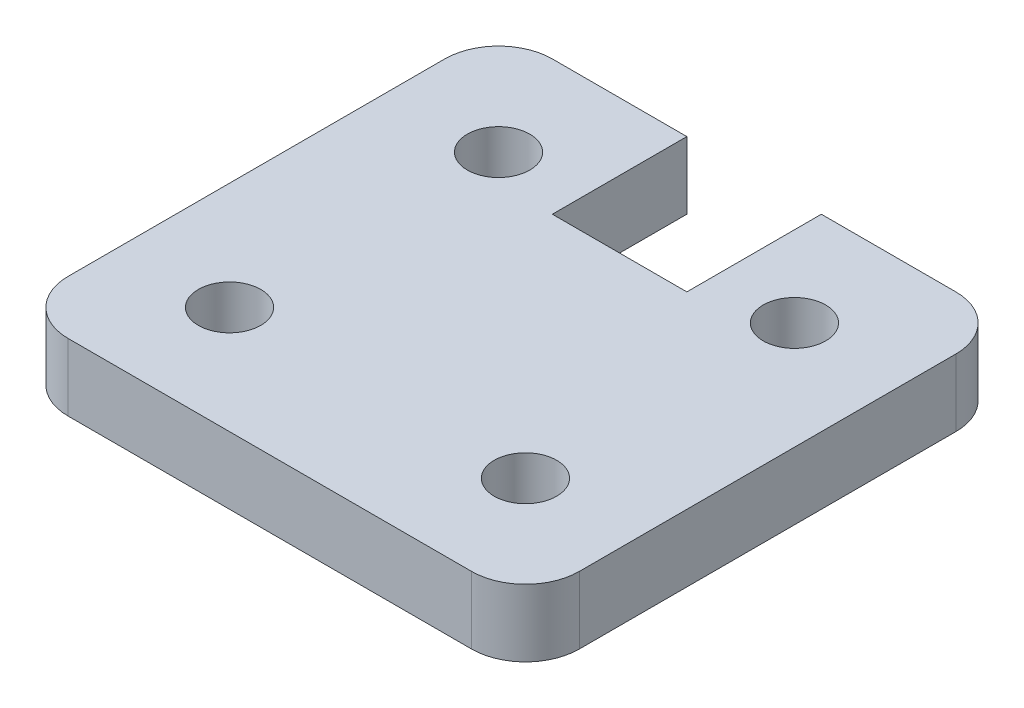
SolidWorks part; units mm, degrees
ref_plane "Front Plane" through (0, 0, 0) normal (0, 0, 1) x (1, 0, 0)
ref_plane "Top Plane" through (0, 0, 0) normal (0, 1, 0) x (1, 0, 0)
ref_plane "Right Plane" through (0, 0, 0) normal (1, 0, 0) x (0, 0, -1)
sketch "Sketch1" plane through (0, 0, 0) normal (0, 1, 0) x (1, 0, 0)
  line L1 (-12.065, -11.43) -> (12.065, -11.43)
  line L2 (-12.065, -11.43) -> (-12.065, 11.43)
  line L3 (-12.065, 11.43) -> (12.065, 11.43)
  line L4 (12.065, -11.43) -> (12.065, 11.43)
  line L5 (-12.065, -11.43) -> (12.065, 11.43) construction
  line L6 (-12.065, 11.43) -> (12.065, -11.43) construction
  point P0 (0, 0)
  dimension "D1" = 22.86
  dimension "D2" = 24.13
extrude "Boss-Extrude1" add sketch "Sketch1" along normal blind 3.175
sketch "Sketch2" plane through (0, 3.175, 0) normal (0, 1, 0) x (1, 0, 0)
  line L0 (12.065, 11.43) -> (-12.065, 11.43) construction
  line L1 (-12.065, 11.43) -> (-12.065, -11.43) construction
  line L2 (0, -11.43) -> (0, 11.43) construction
  line L3 (-12.065, -11.43) -> (12.065, -11.43) construction
  line L4 (-12.065, 0) -> (12.065, 0) construction
  line L5 (12.065, -11.43) -> (12.065, 11.43) construction
  circle A0 centre (-6.985, 6.35) radius 1.4732
  circle A1 centre (-6.985, -6.35) radius 1.4732
  circle A2 centre (6.985, -6.35) radius 1.4732
  circle A3 centre (6.985, 6.35) radius 1.4732
  point P2 (-8.4582, 6.35)
  point P3 (-6.985, 7.8232)
  dimension "D1" = 2.9464
  dimension "D2" = 13.97
  dimension "D3" = 12.7
extrude "Cut-Extrude1" cut sketch "Sketch2" against normal through all
fillet "Fillet1" radius 2.54 4 edges at (-12.065, 1.5875, -11.43) (12.065, 1.5875, -11.43) (12.065, 1.5875, 11.43) (-12.065, 1.5875, 11.43)
sketch "Sketch3" plane through (0, 3.175, 0) normal (0, 1, 0) x (1, 0, 0)
  line L0 (9.525, 11.43) -> (-9.525, 11.43) construction
  line L1 (3.175, 11.43) -> (-3.175, 11.43)
  line L2 (3.175, 11.43) -> (3.175, 5.08)
  line L3 (3.175, 5.08) -> (-3.175, 5.08)
  line L4 (-3.175, 11.43) -> (-3.175, 5.08)
  line L5 (3.175, 12.7) -> (3.175, -11.43) construction
  dimension "D1" = 6.35
  dimension "D2" = 6.35
extrude "Cut-Extrude2" cut sketch "Sketch3" against normal through all
